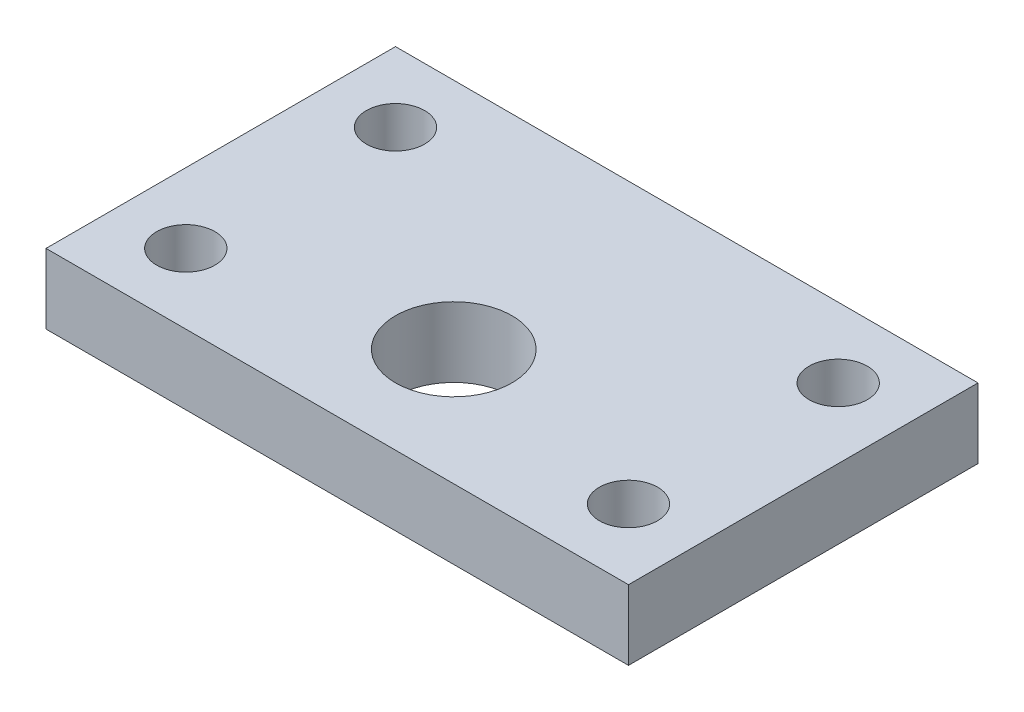
SolidWorks part; units mm, degrees
ref_plane "Front Plane" through (0, 0, 0) normal (0, 0, 1) x (1, 0, 0)
ref_plane "Top Plane" through (0, 0, 0) normal (0, 1, 0) x (1, 0, 0)
ref_plane "Right Plane" through (0, 0, 0) normal (1, 0, 0) x (0, 0, -1)
sketch "Sketch1" plane through (0, 0, 0) normal (0, 1, 0) x (1, 0, 0)
  line L0 (125, 180.1294) -> (125, -61.1648) construction
  line L1 (0, 0) -> (250, 0)
  line L2 (0, 0) -> (0, 150)
  line L3 (0, 150) -> (250, 150)
  line L4 (250, 0) -> (250, 150)
  circle A0 centre (30, 30) radius 12.5
  circle A1 centre (30, 120) radius 12.5
  circle A2 centre (220, 120) radius 12.5
  circle A3 centre (220, 30) radius 12.5
  circle A4 centre (125, 50) radius 25
  dimension "D3" = 30
  dimension "D6" = 25
  dimension "D7" = 50
  dimension "D8" = 50
  dimension "D1" = 250
  dimension "D2" = 150
  dimension "D4" = 30
  dimension "D5" = 90
extrude "Boss-Extrude1" add sketch "Sketch1" along normal blind 30
